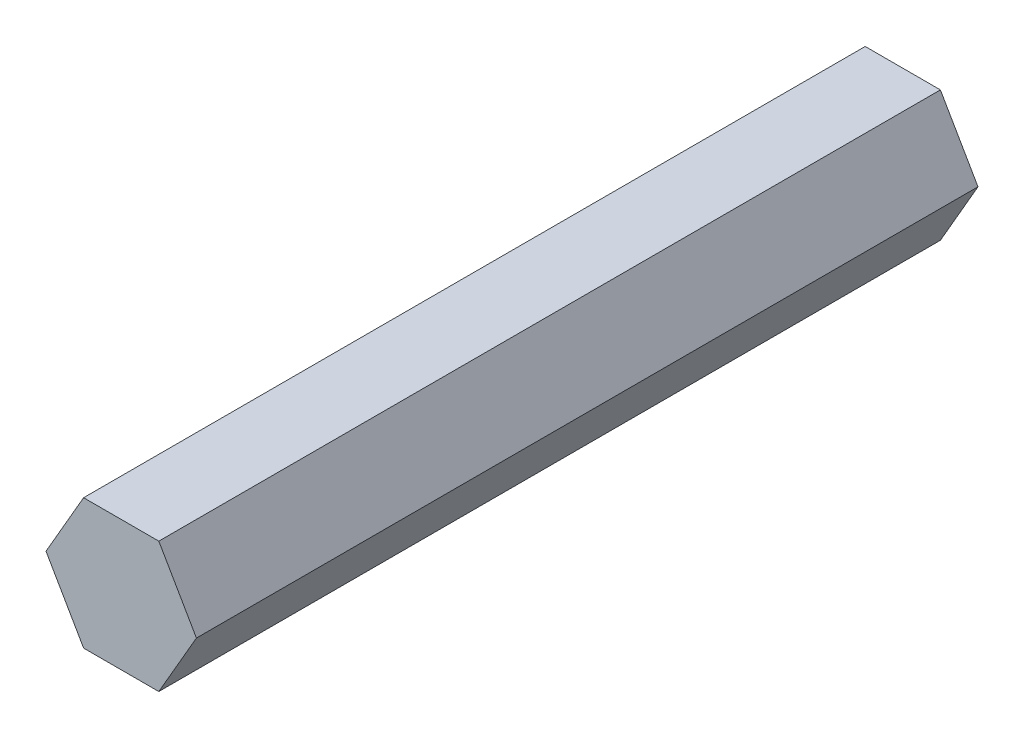
SolidWorks part; units mm, degrees
ref_plane "Front Plane" through (0, 0, 0) normal (0, 0, 1) x (1, 0, 0)
ref_plane "Top Plane" through (0, 0, 0) normal (0, 1, 0) x (1, 0, 0)
ref_plane "Right Plane" through (0, 0, 0) normal (1, 0, 0) x (0, 0, -1)
sketch "Sketch1" plane through (0, 0, 0) normal (0, 0, 1) x (1, 0, 0)
  line L1 (7.3323, 0) -> (3.6662, 6.35)
  line L2 (3.6662, 6.35) -> (-3.6662, 6.35)
  line L3 (-3.6662, 6.35) -> (-7.3323, 0)
  line L4 (-7.3323, 0) -> (-3.6662, -6.35)
  line L5 (-3.6662, -6.35) -> (3.6662, -6.35)
  line L6 (3.6662, -6.35) -> (7.3323, 0)
  circle A0 centre (0, 0) radius 6.35 construction
  dimension "D1" = 12.7
extrude "Boss-Extrude1" add sketch "Sketch1" along normal blind 76.2
